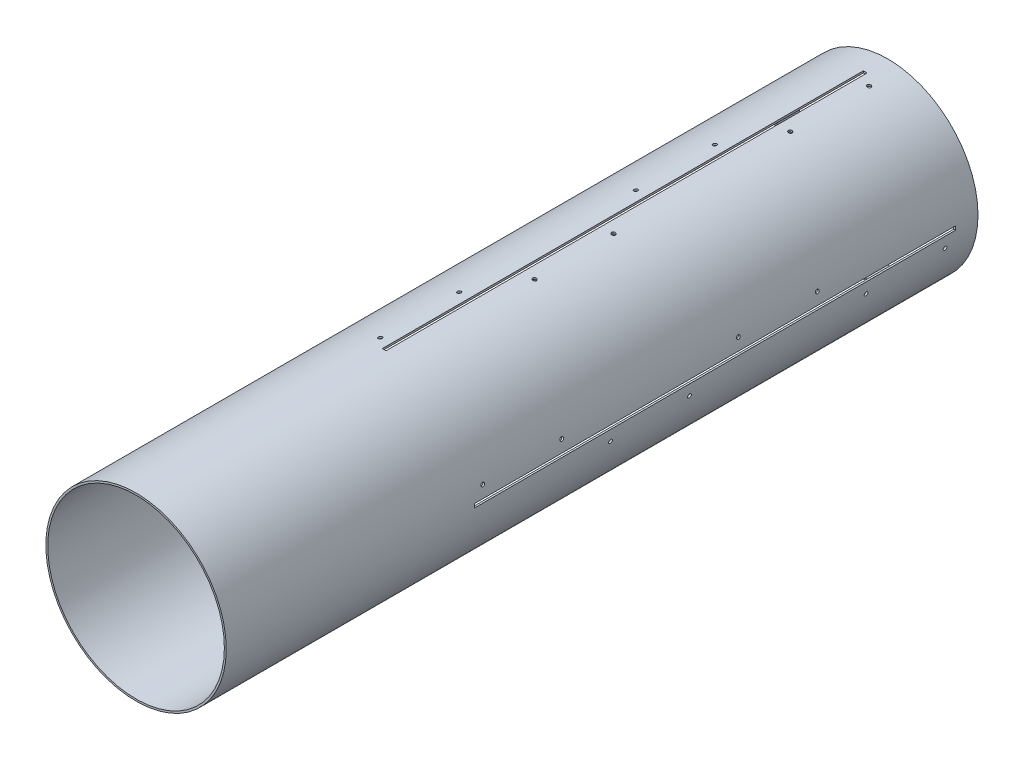
SolidWorks part; units mm, degrees
material "6061-T6 (SS)"
ref_plane "Front Plane" through (0, 0, 0) normal (0, 0, 1) x (1, 0, 0)
ref_plane "Top Plane" through (0, 0, 0) normal (0, 1, 0) x (1, 0, 0)
ref_plane "Right Plane" through (0, 0, 0) normal (1, 0, 0) x (0, 0, -1)
sketch "Sketch1" plane through (0, 0, 0) normal (0, 0, 1) x (1, 0, 0)
  circle A0 centre (0, 0) radius 152.4
  dimension "D1" = 304.8
extrude "Boss-Extrude1" add sketch "Sketch1" along normal blind 1270 contours A0
ref_plane "Plane2" [suppressed] through (19.6284, -151.1307, 0) normal (0.1288, -0.9917, 0) x (0, 0, -1)
ref_plane "Plane1" [suppressed] through (-19.6284, -151.1307, 0) normal (-0.1288, -0.9917, 0) x (0, 0, -1)
sketch "Sketch2" plane through (0, 0, 1270) normal (0, 0, 1) x (1, 0, 0)
  circle A0 centre (0, 0) radius 149.225
  dimension "D1" = 298.45
extrude "Cut-Extrude1" cut sketch "Sketch2" against normal blind 1270 contours A0
sketch "Sketch3" plane through (0, 0, 0) normal (0, 1, 0) x (1, 0, 0)
  line L0 (0, 0) -> (0, -25.4) construction
sketch "Sketch4" plane through (0, 0, 0) normal (0, 1, 0) x (1, 0, 0)
  line L1 (-152.4, -1270) -> (152.4, -1270) construction
  line L2 (0, -1270) -> (0, -1263.65) construction
  circle A0 centre (0, -1263.65) radius 3.175
  dimension "D1" = 6.35
  dimension "D2" = 6.35
extrude "Cut-Extrude2" [suppressed] cut sketch "Sketch4" against normal blind 300.482
pattern_circular "CirPattern1" [suppressed] count 8 over 360
sketch "Sketch6" plane through (0, 0, 0) normal (0, 1, 0) x (1, 0, 0)
  line L1 (-3.175, -850.9) -> (3.175, -850.9)
  line L3 (-3.175, -38.1) -> (3.175, -38.1)
  line L4 (3.175, -850.9) -> (3.175, -38.1)
  line L5 (152.4, 0) -> (-152.4, 0) construction
  line L6 (0, -25.4) -> (0, -850.9) construction
  line L7 (-3.175, -850.9) -> (-3.175, -38.1)
  point P11 (0, -38.1)
  dimension "D2" = 6.35
  dimension "D3" = 38.1
  dimension "D1" = 812.8
extrude "Cut-Extrude3" cut sketch "Sketch6" against normal blind 152.4
pattern_circular "CirPattern2" count 4 over 360 about axis through (0, 0, 0) along (0, 0, 1) of "Cut-Extrude3"
sketch "Sketch7" plane through (-20.3677, 146.788, 850.9) normal (-0.1383, 0.9904, 0) x (0.9904, 0.1383, 0)
  circle A0 centre (-1.4845, 149.225) radius 3.175 construction
  circle A1 centre (-1.4845, 15.875) radius 3.175 construction
  circle A2 centre (-1.4845, 149.225) radius 3.175
  circle A3 centre (-1.4845, 15.875) radius 3.175
  circle A4 centre (-1.4845, 447.675) radius 3.175 construction
  circle A5 centre (-1.4845, 581.025) radius 3.175 construction
  circle A6 centre (-1.4845, 447.675) radius 3.175
  circle A7 centre (-1.4845, 581.025) radius 3.175
extrude "Cut-Extrude4" cut sketch "Sketch7" along normal up to surface (4.1383 mm away)
sketch "Sketch8" plane through (20.3677, 146.788, 469.9) normal (0.1383, 0.9904, 0) x (-0.9904, 0.1383, 0)
  circle A0 centre (-1.4845, -282.575) radius 3.175 construction
  circle A1 centre (-1.4845, -415.925) radius 3.175 construction
  circle A2 centre (-1.4845, 15.875) radius 3.175 construction
  circle A3 centre (-1.4845, 149.225) radius 3.175 construction
  circle A4 centre (-1.4845, -282.575) radius 3.175
  circle A5 centre (-1.4845, -415.925) radius 3.175
  circle A6 centre (-1.4845, 15.875) radius 3.175
  circle A7 centre (-1.4845, 149.225) radius 3.175
extrude "Cut-Extrude5" cut sketch "Sketch8" along normal up to surface (4.1949 mm away)
pattern_circular "CirPattern3" count 4 over 360 about axis through (0, 0, 0) along (0, 0, 1) of "Cut-Extrude5", "Cut-Extrude4"
equation "\"Rocket Diameter\"= 12in"
equation "\"D1@Sketch1\"=\"Rocket Diameter\""
equation "\"Airframe Thickness\"= 0.125in"
equation "\"Length\"= 50in"
equation "\"D1@Boss-Extrude1\"=\"Length\""
equation "\"D1@Cut-Extrude1\"=\"Length\""
equation "\"Bolt Diameter\"= 0.25in"
equation "\"D1@Sketch2\"= \"Rocket Diameter\"-\"Airframe Thickness\"*2"
equation "\"D1@Sketch4\"=\"Bolt Diameter\""
equation "\"Fin Root Chord\"= 32in"
equation "\"Fin Thickness\"= .25in"
equation "\"D2@Sketch6\"=\"Fin Thickness\""
equation "\"D1@Sketch6\"=\"Fin Root Chord\""
